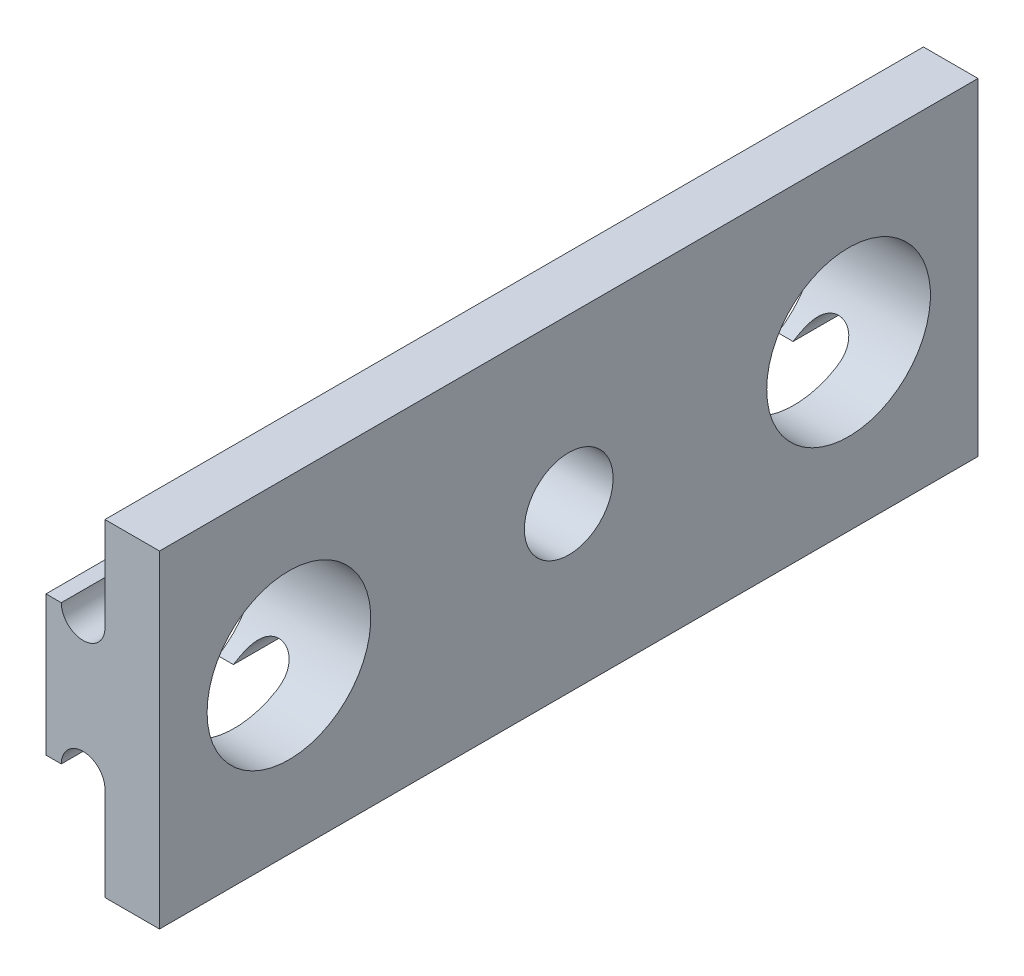
SolidWorks part; units mm, degrees
ref_plane "Front Plane" through (0, 0, 0) normal (0, 0, 1) x (1, 0, 0)
ref_plane "Top Plane" through (0, 0, 0) normal (0, 1, 0) x (1, 0, 0)
ref_plane "Right Plane" through (0, 0, 0) normal (1, 0, 0) x (0, 0, -1)
sketch "Sketch1" plane through (0, 0, 0) normal (0, 0, 1) x (1, 0, 0)
  line L0 (0, -9.525) -> (0, 9.525)
  line L1 (0, 9.525) -> (-3.175, 9.525)
  line L2 (-3.175, 9.525) -> (-3.175, 4.064)
  line L3 (-5.715, 4.064) -> (-6.604, 4.064)
  line L4 (-6.604, 4.064) -> (-6.604, -4.064)
  line L5 (-6.604, 0) -> (0, 0) construction
  line L6 (-5.715, -4.064) -> (-6.604, -4.064)
  line L7 (-3.175, -9.525) -> (-3.175, -4.064)
  line L8 (0, -9.525) -> (-3.175, -9.525)
  arc A0 (-3.175, 4.064) -> (-5.715, 4.064) centre (-4.445, 4.064) cw
  arc A1 (-3.175, -4.064) -> (-5.715, -4.064) centre (-4.445, -4.064) ccw
  point P7 (-5.201, 6.1484)
  dimension "D1" = 1.27
  dimension "D2" = 9.525
  dimension "D3" = 3.175
  dimension "D4" = 3.429
  dimension "D5" = 4.064
extrude "Boss-Extrude1" add sketch "Sketch1" along normal mid plane 47.625
sketch "Sketch2" plane through (-6.604, 0, 0) normal (-1, 0, 0) x (0, 0, 1)
  line L0 (-16.2814, 0) -> (16.2814, 0) construction
  circle A0 centre (16.2814, 0) radius 2.5797
  circle A1 centre (-16.2814, 0) radius 2.5797
  circle A2 centre (0, 0) radius 2.5797
  dimension "D1" = 5.1594
  dimension "D2" = 32.5628
extrude "Cut-Extrude1" cut sketch "Sketch2" against normal through all
sketch "Sketch3" plane through (-6.604, 0, 0) normal (-1, 0, 0) x (0, 0, 1)
  circle A0 centre (-16.2814, 0) radius 4.7625
  circle A1 centre (16.2814, 0) radius 4.7625
  dimension "D1" = 9.525
extrude "Cut-Extrude2" cut sketch "Sketch3" against normal through all
